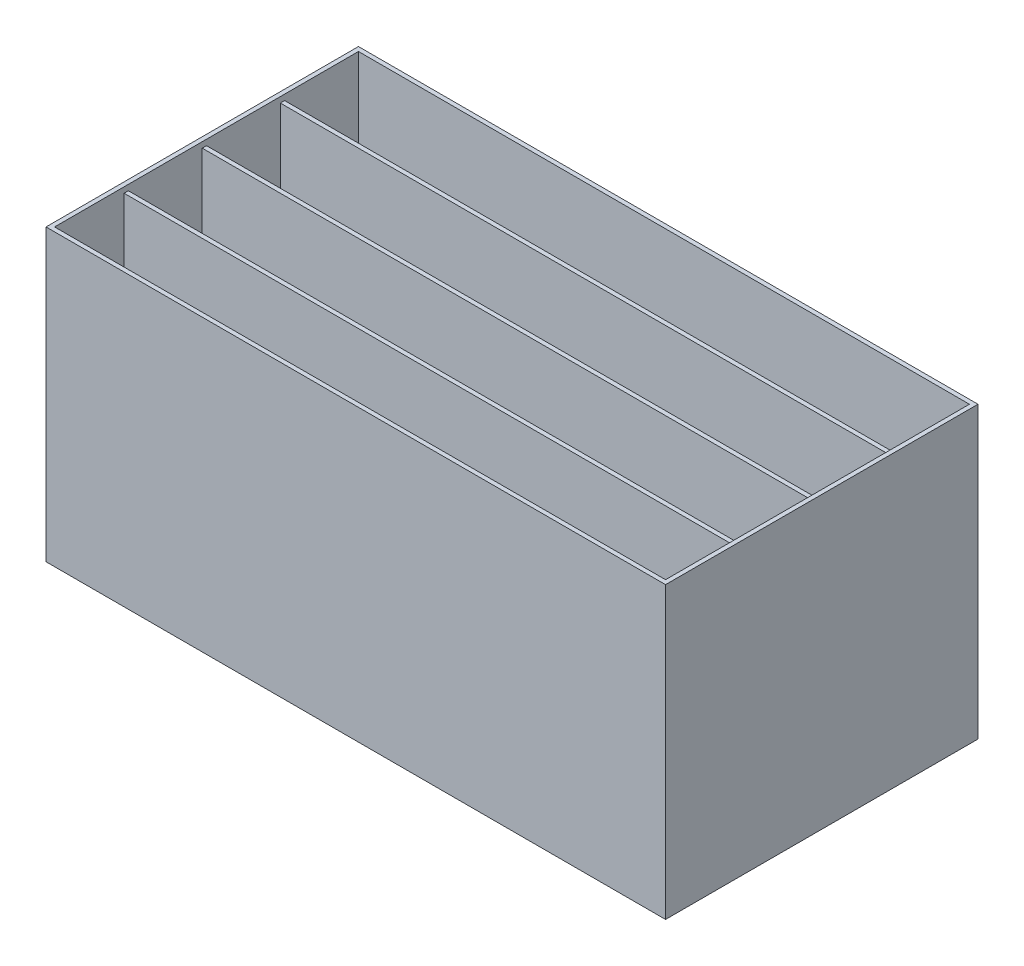
SolidWorks part; units mm, degrees
material "Glass"
ref_plane "Front Plane" through (0, 0, 0) normal (0, 0, 1) x (1, 0, 0)
ref_plane "Top Plane" through (0, 0, 0) normal (0, 1, 0) x (1, 0, 0)
ref_plane "Right Plane" through (0, 0, 0) normal (1, 0, 0) x (0, 0, -1)
ref_plane "Plane1" through (0, 391.414, 0) normal (0, 1, 0) x (1, 0, 0)
sketch "Sketch1" plane through (0, 0, 0) normal (0, 1, 0) x (1, 0, 0)
  line L1 (0, 0) -> (919.1625, 0)
  line L2 (0, 0) -> (0, 463.55)
  line L3 (0, 463.55) -> (919.1625, 463.55)
  line L4 (919.1625, 0) -> (919.1625, 463.55)
  dimension "D1" = 919.1625
  dimension "D2" = 463.55
extrude "Boss-Extrude1" add sketch "Sketch1" along normal blind 430.2125
shell "Shell1" thickness 6.35
sketch "Sketch2" plane through (0, 391.414, 0) normal (0, 1, 0) x (1, 0, 0)
  line L0 (6.35, 457.2) -> (6.35, 6.35) construction
  line L1 (6.35, 347.6625) -> (912.8125, 347.6625)
  line L2 (6.35, 347.6625) -> (6.35, 341.3125)
  line L3 (6.35, 341.3125) -> (912.8125, 341.3125)
  line L4 (912.8125, 347.6625) -> (912.8125, 341.3125)
  line L5 (912.8125, 6.35) -> (912.8125, 457.2) construction
  line L6 (6.35, 344.4875) -> (-41.0429, 344.4875) construction
  line L7 (912.8125, 457.2) -> (6.35, 457.2) construction
  line L8 (6.35, 231.775) -> (6.35, 225.425)
  line L9 (6.35, 231.775) -> (912.8125, 231.775)
  line L10 (912.8125, 231.775) -> (912.8125, 225.425)
  line L11 (6.35, 225.425) -> (912.8125, 225.425)
  line L12 (6.35, 115.8875) -> (6.35, 109.5375)
  line L13 (6.35, 115.8875) -> (912.8125, 115.8875)
  line L14 (912.8125, 115.8875) -> (912.8125, 109.5375)
  line L15 (6.35, 109.5375) -> (912.8125, 109.5375)
  line L16 (6.35, 228.6) -> (-36.5036, 228.6) construction
  line L18 (6.35, 112.7125) -> (-55.5434, 112.7125) construction
  dimension "D1" = 6.35
  dimension "D2" = 112.7125
  dimension "D4" = 115.8875
  dimension "D3" = 3
extrude "Boss-Extrude2" add sketch "Sketch2" against normal up to next and the other way blind 30.48
sketch "Sketch4" plane through (0, 430.2125, 0) normal (0, 1, 0) x (1, 0, 0)
  line L0 (6.35, 402.4312) -> (175.3542, 402.4312) construction
  line L1 (6.35, 457.2) -> (6.35, 347.6625) construction
  line L3 (6.35, 286.5437) -> (182.0227, 286.5437) construction
  line L4 (6.35, 341.3125) -> (6.35, 231.775) construction
  line L5 (6.35, 170.6562) -> (182.0227, 170.6562) construction
  line L6 (6.35, 225.425) -> (6.35, 115.8875) construction
  line L7 (6.35, 57.9438) -> (182.0227, 57.9438) construction
  line L8 (6.35, 109.5375) -> (6.35, 6.35) construction
